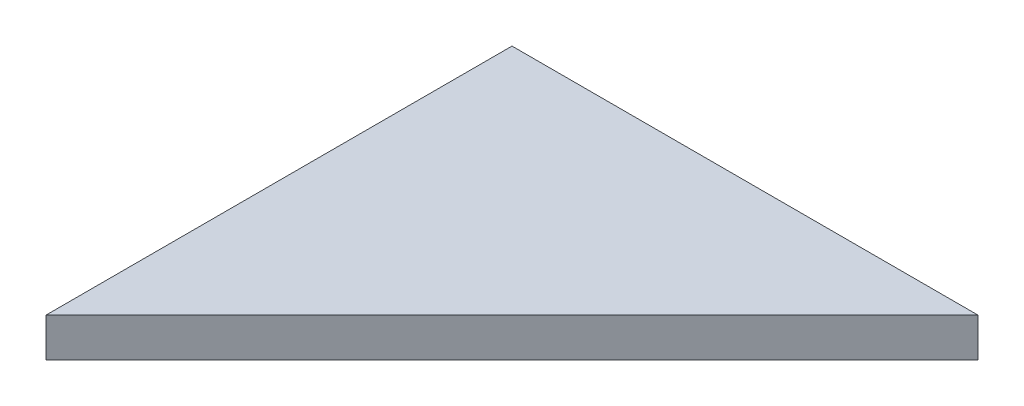
SolidWorks part; units mm, degrees
material "ASTM A36 Steel"
ref_plane "Front Plane" through (0, 0, 0) normal (0, 0, 1) x (1, 0, 0)
ref_plane "Top Plane" through (0, 0, 0) normal (0, 1, 0) x (1, 0, 0)
ref_plane "Right Plane" through (0, 0, 0) normal (1, 0, 0) x (0, 0, -1)
sketch "Sketch1" plane through (0, 0, 0) normal (0, 1, 0) x (1, 0, 0)
  line L0 (38.1, 0) -> (0, 0)
  line L1 (-55, 0) -> (55, 0) construction
  line L2 (0, 0) -> (0, -38.1)
  line L3 (0, -55) -> (0, 55) construction
  line L4 (0, -38.1) -> (38.1, 0)
  dimension "D1" = 38.1
  dimension "D2" = 38.1
extrude "Boss-Extrude1" add sketch "Sketch1" along normal mid plane 3.175
sketch3d "TAG"
  line L0 (0, 1.5875, 0) -> (0, -1.5875, 0) construction
  line L1 (0, 1.5875, 0) -> (0, 1.5875, 38.1) construction
  line L2 (38.1, 1.5875, 0) -> (0, 1.5875, 0) construction
  line L3 (0, 1.5875, 0) -> (0, -1.5875, 0)
  line L4 (0, 1.5875, 0) -> (0, 1.5875, 38.1)
  line L5 (38.1, 1.5875, 0) -> (0, 1.5875, 0)
  dimension "D1" = 3.175
  dimension "D2" = 38.1
  dimension "D3" = 38.1
